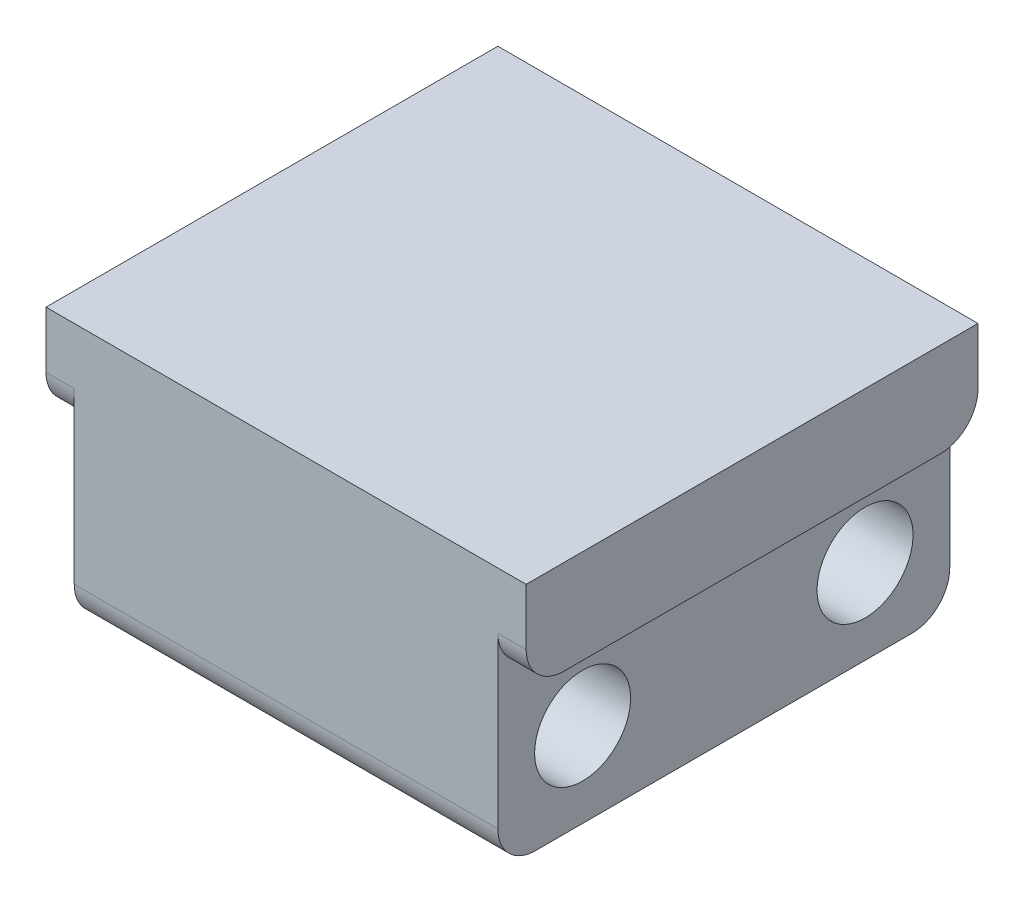
SolidWorks part; units mm, degrees
material "ABS"
ref_plane "Front Plane" through (0, 0, 0) normal (0, 0, 1) x (1, 0, 0)
ref_plane "Top Plane" through (0, 0, 0) normal (0, 1, 0) x (1, 0, 0)
ref_plane "Right Plane" through (0, 0, 0) normal (1, 0, 0) x (0, 0, -1)
sketch "Sketch1" plane through (0, 0, 0) normal (0, 0, 1) x (1, 0, 0)
  line L0 (0, 0) -> (0, 18.7675) construction
  line L1 (11.25, 0) -> (-11.25, 0)
  line L2 (-11.25, 0) -> (-11.25, 9)
  line L3 (-11.25, 9) -> (-12.75, 9)
  line L4 (-12.75, 9) -> (-12.75, 14)
  line L5 (12.75, 9) -> (12.75, 14)
  line L6 (11.25, 9) -> (12.75, 9)
  line L7 (11.25, 0) -> (11.25, 9)
  line L8 (-12.75, 14) -> (12.75, 14)
  dimension "D1" = 9
  dimension "D2" = 5
  dimension "D3" = 22.5
  dimension "D4" = 1.5
extrude "Main Body" add sketch "Sketch1" along normal mid plane 24
sketch "Sketch2" plane through (-11.25, 0, 0) normal (-1, 0, 0) x (0, 0, 1)
  line L0 (-12, 4.5) -> (12, 4.5) construction
  line L1 (-12, 9) -> (-12, 0) construction
  line L2 (12, 9) -> (12, 0) construction
  line L3 (0, 0) -> (0, 9) construction
  line L4 (12, 0) -> (-12, 0) construction
  line L5 (12, 9) -> (-12, 9) construction
  circle A0 centre (-7.5, 4.5) radius 2.55
  circle A1 centre (7.5, 4.5) radius 2.55
  dimension "D2" = 5.1
  dimension "D1" = 15
extrude "Clearance - M3 Inserts" cut sketch "Sketch2" against normal through all
fillet "Contouring" radius 2 6 edges at (12, 9, 12) (-12, 9, 12) (12, 9, -12) (-12, 9, -12) (0, 0, -12) (0, 0, 12)
